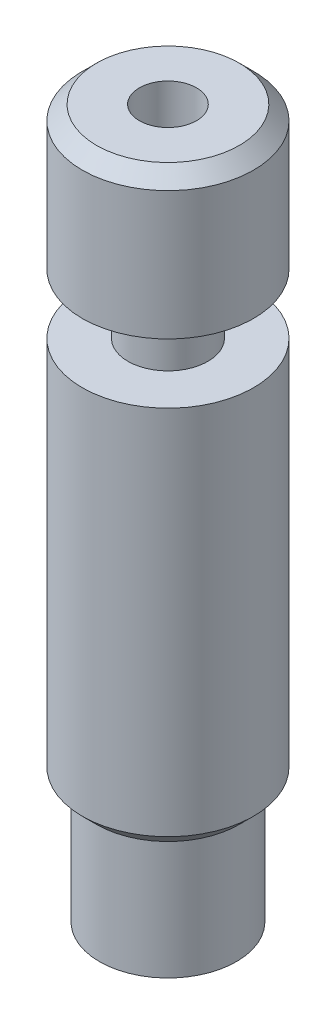
SolidWorks part; units mm, degrees
material "AISI 316 Annealed Stainless Steel Bar (SS)"
ref_plane "Front Plane" through (0, 0, 0) normal (0, 0, 1) x (1, 0, 0)
ref_plane "Top Plane" through (0, 0, 0) normal (0, 1, 0) x (1, 0, 0)
ref_plane "Right Plane" through (0, 0, 0) normal (1, 0, 0) x (0, 0, -1)
sketch "Sketch1" plane through (0, 0, 0) normal (0, 0, 1) x (1, 0, 0)
  line L0 (0, 12.55) -> (0, -12.55) construction
  line L1 (1, -12.15) -> (1, 12.55)
  line L2 (1, 12.55) -> (2.5, 12.55)
  line L3 (3, 12.05) -> (3, 7.55)
  line L4 (3, 7.55) -> (1.4, 7.55)
  line L5 (1.4, 7.55) -> (1.4, 5.45)
  line L6 (1.4, 5.45) -> (3, 5.45)
  line L7 (2.4, -12.2613) -> (2.4, -8.05)
  line L8 (1.4, -12.55) -> (1.9, -12.55)
  line L9 (2.4, -8.05) -> (2.5, -8.05)
  line L10 (3, -7.55) -> (3, 5.45)
  line L11 (2.5, 12.55) -> (3, 12.05)
  line L12 (2.5, -8.05) -> (3, -7.55)
  line L13 (1.4, -12.55) -> (1, -12.15)
  line L14 (1.9, -12.55) -> (2.4, -12.2613)
  point P3 (1, -12.55)
  point P6 (3, 12.55)
  point P13 (3, -8.05)
  dimension "D1" = 25.1
  dimension "D2" = 1
  dimension "D3" = 5
  dimension "D4" = 2.1
  dimension "D5" = 6
  dimension "D6" = 20.6
  dimension "D7" = 4.8
  dimension "D8" = 0.4
  dimension "D9" = 3.8
  dimension "D10" = 30
revolve "Revolve1" add sketch "Sketch1" angle 360 about L0
